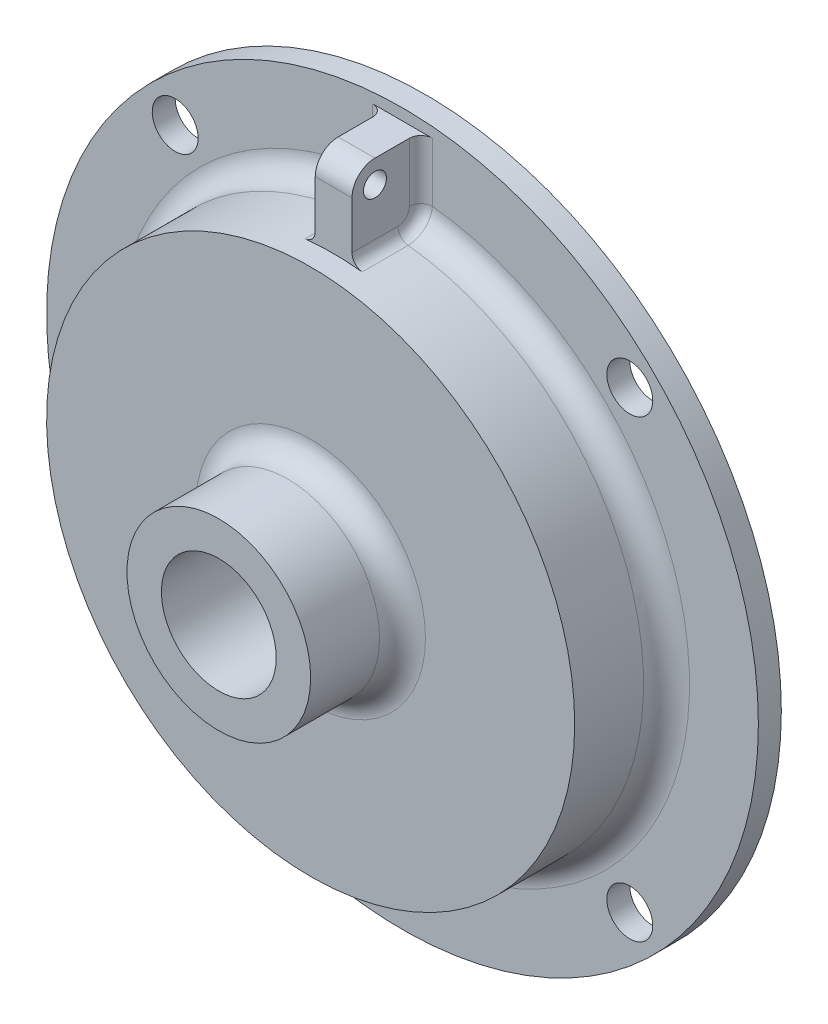
SolidWorks part; units mm, degrees
material "PW40:6:Sc:0:Re:24:"
ref_plane "Front" through (0, 0, 0) normal (0, 0, 1) x (1, 0, 0)
ref_plane "Top" through (0, 0, 0) normal (0, 1, 0) x (1, 0, 0)
ref_plane "Right" through (0, 0, 0) normal (1, 0, 0) x (0, 0, -1)
other "Configuration Table"
sketch "Sketch1" plane through (0, 0, 0) normal (0, 0, 1) x (1, 0, 0)
  circle A0 centre (0, 0) radius 49.2125
  dimension "D1" = 98.425
extrude "Base-Extrude" add sketch "Sketch1" along normal blind 3.175
sketch "Sketch5" plane through (0, 0, 3.175) normal (0, 0, 1) x (1, 0, 0)
  line L0 (31.4309, 31.4309) -> (0, 0) construction
  line L1 (0, 0) -> (44.45, 0) construction
  circle A0 centre (0, 0) radius 44.45 construction
  circle A1 centre (31.4309, 31.4309) radius 3.175
  dimension "D1" = 88.9
  dimension "D2" = 6.35
  dimension "D3" = 45
extrude "Cut-Extrude2" cut sketch "Sketch5" against normal through all
pattern_circular "CirPattern1" count 4 every 90 about axis through (0, 0, 0) along (0, 0, 1) of "Cut-Extrude2"
sketch "Sketch2" plane through (0, 0, 3.175) normal (0, 0, 1) x (1, 0, 0)
  circle A0 centre (0, 0) radius 36.5125
  dimension "D1" = 73.025
extrude "Boss-Extrude1" add sketch "Sketch2" along normal blind 12.7
sketch "Sketch3" plane through (0, 0, 15.875) normal (0, 0, 1) x (1, 0, 0)
  circle A0 centre (0, 0) radius 12.7
  dimension "D1" = 25.4
extrude "Boss-Extrude2" add sketch "Sketch3" along normal blind 12.7
fillet "Fillet1" radius 3.175 2 edges at (36.5125, 0, 3.175) (12.7, 0, 15.875)
sketch "Sketch6" plane through (0, 0, 0) normal (0, 1, 0) x (1, 0, 0)
  line L0 (-2.54, -3.175) -> (-2.54, -12.7)
  line L1 (-39.6875, -3.175) -> (39.6875, -3.175) construction
  line L2 (-2.54, -3.175) -> (2.54, -3.175)
  line L3 (-49.2125, -3.175) -> (49.2125, -3.175) construction
  line L4 (2.54, -3.175) -> (2.54, -12.7)
  line L5 (-2.54, -12.7) -> (2.54, -12.7)
  line L6 (0, 0) -> (0, -38.11) construction
  line L7 (0, -3.175) -> (0, 0) construction
  dimension "D1" = 5.08
  dimension "D2" = 9.525
extrude "Boss-Extrude3" add sketch "Sketch6" along normal blind 47.625
sketch "Sketch4" plane through (0, 0, 28.575) normal (0, 0, 1) x (1, 0, 0)
  circle A0 centre (0, 0) radius 7.9375
  dimension "D1" = 15.875
extrude "Cut-Extrude1" cut sketch "Sketch4" against normal through all
fillet "Fillet2" radius 3.175 1 edges at (0, 47.625, 12.7)
sketch "Sketch7" plane through (2.54, 0, 0) normal (1, 0, 0) x (0, 0, -1)
  circle A0 centre (-9.525, 44.45) radius 1.5875
  arc A1 (-9.525, 47.625) -> (-12.7, 44.45) centre (-9.525, 44.45) ccw construction
  dimension "D1" = 3.175
extrude "Cut-Extrude3" cut sketch "Sketch7" against normal up to next
fillet "Fillet3" radius 1.5875 6 edges at (2.54, 41.6917, 8.7475) (-2.54, 41.6917, 8.7475) (-2.54, 36.424, 9.525) (-2.54, 43.6156, 3.175) (2.54, 43.6156, 3.175) (2.54, 36.424, 9.525)
